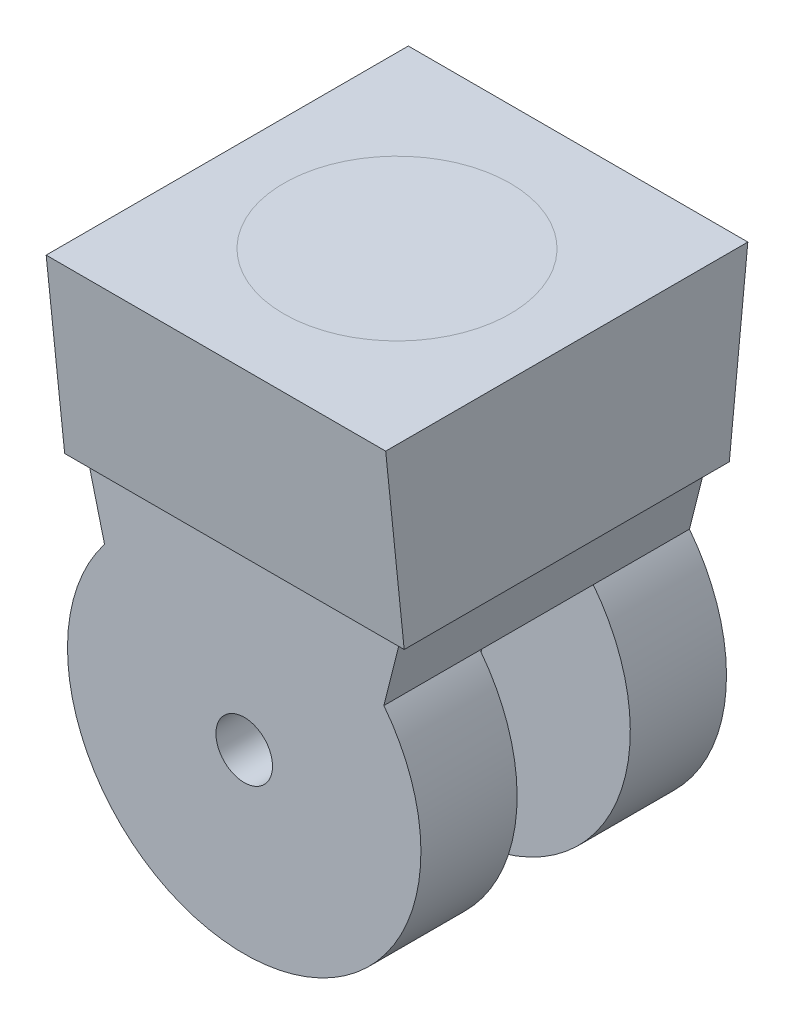
SolidWorks part; units mm, degrees
ref_plane "Alzado" through (0, 0, 0) normal (0, 0, 1) x (1, 0, 0)
ref_plane "Planta" through (0, 0, 0) normal (0, 1, 0) x (1, 0, 0)
ref_plane "Vista lateral" through (0, 0, 0) normal (1, 0, 0) x (0, 0, -1)
sketch "Croquis1" plane through (0, 0, 0) normal (1, 0, 0) x (0, 0, -1)
  line L0 (-40.64, 20.32) -> (-36.4861, -20.32)
  line L1 (-36.4861, -20.32) -> (0, -20.32)
  line L2 (40.64, 20.32) -> (36.4861, -20.32)
  line L3 (36.4861, -20.32) -> (0, -20.32)
  line L4 (-40.64, 20.32) -> (40.64, 20.32)
extrude "Saliente-Extruir1" add sketch "Croquis1" along normal mid plane 76.2
sketch "Croquis2" plane through (0, 0, 0) normal (0, 0, 1) x (1, 0, 0)
  line L0 (35.2237, -20.32) -> (31.3489, -35.6876)
  line L1 (38.1, -20.32) -> (-38.1, -20.32) construction
  line L2 (0, 34.8542) -> (0, -59.9788) construction
  line L3 (-35.2237, -20.32) -> (35.2237, -20.32)
  line L4 (-35.2237, -20.32) -> (-31.3489, -35.6876)
  arc A0 (-31.3489, -35.6876) -> (31.3489, -35.6876) centre (0, -59.9788) ccw
extrude "Saliente-Extruir2" add sketch "Croquis2" along normal mid plane 68.58
sketch "Croquis3" plane through (0, 0, 0) normal (0, 0, 1) x (1, 0, 0)
  circle A0 centre (0, -59.9788) radius 39.6588
  dimension "D1" = 79.3175
extrude "Cortar-Extruir1" cut sketch "Croquis3" against normal mid plane 25.4
sketch "Croquis4" plane through (0, 0, 34.29) normal (0, 0, 1) x (1, 0, 0)
  circle A0 centre (0, -59.9788) radius 6.35
  dimension "D1" = 12.7
extrude "Cortar-Extruir2" cut sketch "Croquis4" against normal through all
sketch "Croquis8" plane through (0, 20.32, 0) normal (0, 1, 0) x (1, 0, 0)
  circle A0 centre (0, 0) radius 25.4
  dimension "D1" = 50.8
split line "Línea de partición1"
